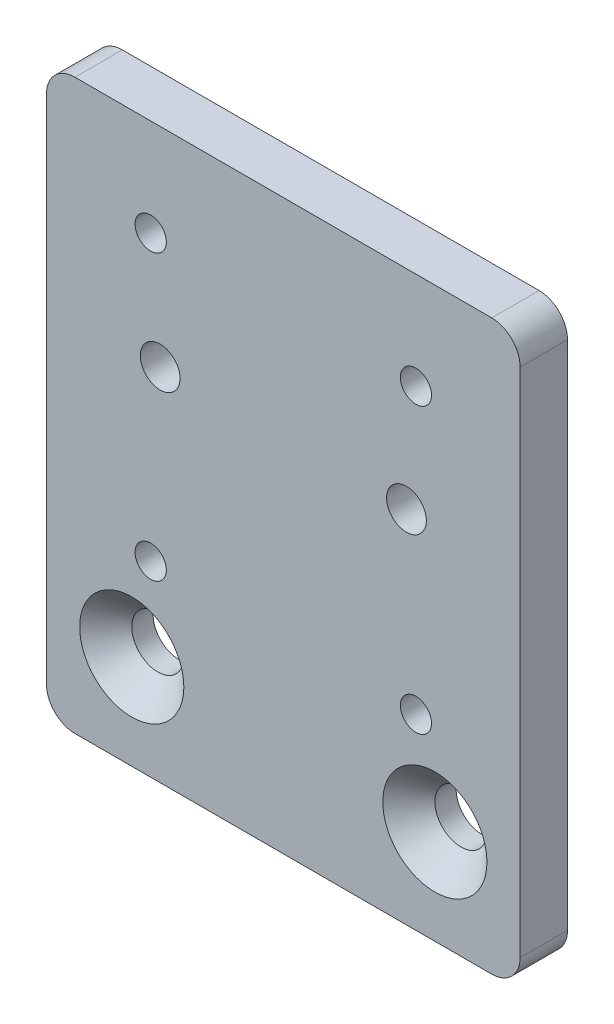
SolidWorks part; units mm, degrees
ref_plane "Ebene vorne" through (0, 0, 0) normal (0, 0, 1) x (1, 0, 0)
ref_plane "Ebene oben" through (0, 0, 0) normal (0, 1, 0) x (1, 0, 0)
ref_plane "Ebene rechts" through (0, 0, 0) normal (1, 0, 0) x (0, 0, -1)
sketch "Skizze1" plane through (0, 0, 0) normal (0, 0, 1) x (1, 0, 0)
  line L0 (55, 0) -> (-55, 0) construction
  line L1 (25, 0) -> (-25, 0)
  line L2 (25, 0) -> (25, 60)
  line L3 (25, 60) -> (-25, 60)
  line L4 (-25, 0) -> (-25, 60)
  line L5 (0, -55) -> (0, 55) construction
  line L6 (-25, 10) -> (25, 10) construction
  line L7 (-25, 20) -> (25, 20) construction
  line L8 (-25, 38) -> (25, 38) construction
  line L9 (-25, 19.75) -> (25, 19.75) construction
  line L10 (-25, 49.75) -> (25, 49.75) construction
  point P6 (0, 0)
  point P13 (-25, 19.8483)
  point P14 (25, 19.9992)
  point P15 (0, 0)
  point P16 (0, 0)
  point P17 (0, 0)
  point P20 (0, 0)
  point P21 (0, 0)
  point P24 (0, 0)
  point P25 (0, 0)
  point P28 (0, 0)
  point P29 (0, 0)
  point P30 (-25, 20)
  point P31 (0, 0)
  point P34 (-24.4013, 10)
  point P35 (-25, 10.4878)
  dimension "D1" = 60
  dimension "D2" = 50
  dimension "D3" = 10
  dimension "D4" = 10
  dimension "D5" = 18
  dimension "D6" = 9.75
  dimension "D7" = 30
extrude "Aufsatz-Linear austragen1" add sketch "Skizze1" against normal blind 5
hole_wizard "Formsenkung für M5 Linsensenkschraube mit Schlitz1" positions "Skizze2" profile "Skizze3" countersink size "M5" standard "ISO"
sketch "Skizze2" plane through (0, 0, 0) normal (0, 0, 1) x (1, 0, 0)
  line L0 (-25, 10) -> (25, 10) construction
  line L1 (-25, 0) -> (-25, 60) construction
  line L2 (25, 0) -> (25, 60) construction
  point P0 (-16, 10)
  point P4 (16, 10)
  dimension "D1" = 9
  dimension "D2" = 9
sketch "Skizze3" plane through (-16, 10, 0) normal (1, 0, 0) x (0, -1, 0)
  line L0 (0, 0) -> (0, 21.6524)
  line L1 (0, 21.6524) -> (2.75, 20)
  line L2 (2.75, 20) -> (2.75, 2.75)
  line L3 (2.75, 2.75) -> (5.5, 0)
  line L5 (5.5, 0) -> (0, 0)
  line L6 (-2.75, 2.75) -> (-5.5, 0) construction
  line L10 (0, 21.6524) -> (-2.75, 20) construction
  line L11 (0, -6.35) -> (0, 107.95) construction
  dimension "Bohrerdurchmesser" = 5.5
  dimension "Bohrungstiefe" = 20
  dimension "Senkdurchmesser (Oben)" = 11
  dimension "Senkwinkel (Oben)" = 90
  dimension "Spitzenwinkel" = 118
hole_wizard "Kernloch für M4 Gewinde1" positions "Skizze4" profile "Skizze5" hole size "M4" standard "ISO" end condition through all
sketch "Skizze4" plane through (0, 0, 0) normal (0, 0, 1) x (1, 0, 0)
  line L0 (-25, 19.75) -> (25, 19.75) construction
  line L1 (-25, 49.75) -> (25, 49.75) construction
  line L2 (0, -2.75) -> (0, 2.75) construction
  point P0 (-14, 19.75)
  point P4 (14, 19.75)
  point P6 (-14, 49.75)
  point P10 (14, 49.75)
  point P13 (0, 0)
  point P14 (0, 0)
  dimension "D1" = 14
  dimension "D2" = 14
sketch "Skizze5" plane through (-14, 19.75, 0) normal (1, 0, 0) x (0, -1, 0)
  line L0 (0, 0) -> (0, 5)
  line L1 (0, 5) -> (1.65, 5)
  line L2 (1.65, 5) -> (1.65, 0)
  line L5 (1.65, 0) -> (0, 0)
  line L11 (0, -6.35) -> (0, 107.95) construction
  dimension "Bohrerdurchmesser" = 3.3
  dimension "Bohrungstiefe" = 5
hole_wizard "Kernloch für M5 Gewinde1" positions "Skizze6" profile "Skizze7" hole size "M5" standard "ISO" end condition through all
sketch "Skizze6" plane through (0, 0, 0) normal (0, 0, 1) x (1, 0, 0)
  line L0 (-25, 38) -> (25, 38) construction
  line L2 (-25, 60) -> (-25, 0) construction
  line L3 (25, 0) -> (25, 60) construction
  point P0 (-13, 38)
  point P4 (13, 38)
  point P7 (0, 0)
  point P8 (0, 0)
  dimension "D1" = 12
  dimension "D2" = 12
sketch "Skizze7" plane through (-13, 38, 0) normal (1, 0, 0) x (0, -1, 0)
  line L0 (0, 0) -> (0, 5)
  line L1 (0, 5) -> (2.1, 5)
  line L2 (2.1, 5) -> (2.1, 0)
  line L5 (2.1, 0) -> (0, 0)
  line L11 (0, -6.35) -> (0, 107.95) construction
  dimension "Bohrerdurchmesser" = 4.2
  dimension "Bohrungstiefe" = 5
fillet "Verrundung1" radius 3 4 edges at (25, 60, -2.5) (-25, 60, -2.5) (-25, 0, -2.5) (25, 0, -2.5)
equation "\"D2@Skizze2\"=\"D1@Skizze2\""
equation "\"D2@Skizze4\"=\"D1@Skizze4\""
equation "\"D2@Skizze6\"=\"D1@Skizze6\""
